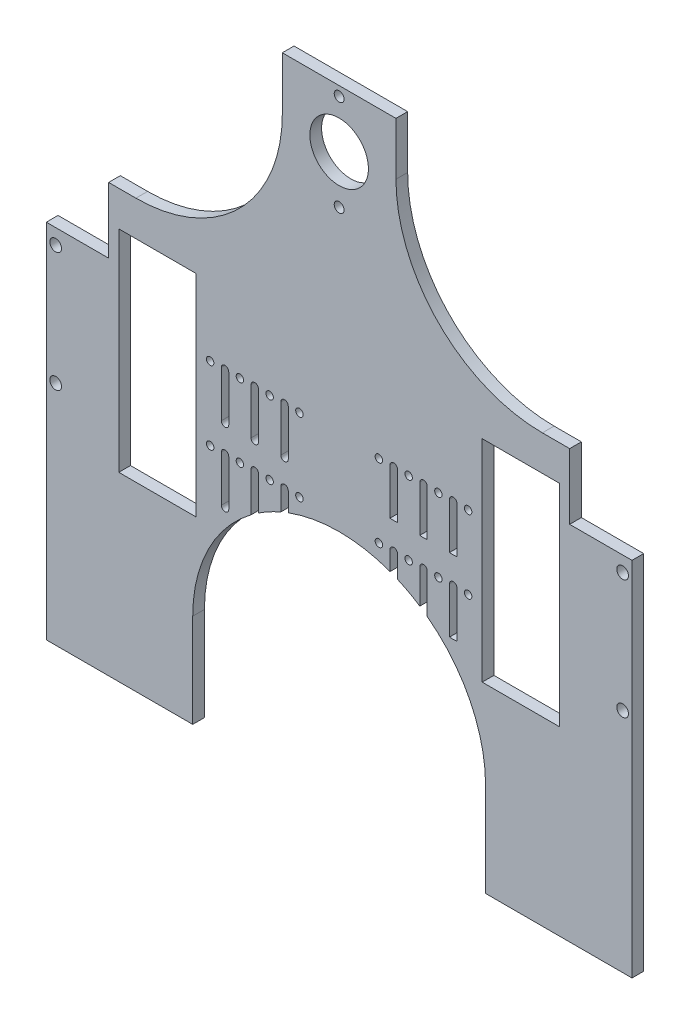
SolidWorks part; units mm, degrees
ref_plane "Front Plane" through (0, 0, 0) normal (0, 0, 1) x (1, 0, 0)
ref_plane "Top Plane" through (0, 0, 0) normal (0, 1, 0) x (1, 0, 0)
ref_plane "Right Plane" through (0, 0, 0) normal (1, 0, 0) x (0, 0, -1)
sketch "Sketch1" plane through (0, 0, 0) normal (0, 0, 1) x (1, 0, 0)
  line L0 (125, 0) -> (125, -350.4) construction
  line L1 (0, 0) -> (250, 0)
  line L2 (0, 0) -> (0, -350.4)
  line L3 (0, -350.4) -> (250, -350.4)
  line L4 (250, 0) -> (250, -350.4)
  line L9 (186.06, -100) -> (219.06, -100)
  line L10 (186.06, -100) -> (186.06, -190)
  line L11 (186.06, -190) -> (219.06, -190)
  line L12 (219.06, -100) -> (219.06, -190)
  line L13 (180.06, -145) -> (228.95, -145) construction
  line L14 (141.96, -129.375) -> (148.31, -129.375) construction
  line L21 (180.06, -145) -> (219.06, -145) construction
  line L25 (141.96, -160.625) -> (148.31, -160.625) construction
  line L32 (148.31, -129.375) -> (148.31, -134.375) construction
  line L33 (146.7225, -129.375) -> (146.7225, -149.0546)
  line L34 (149.8975, -129.375) -> (149.8975, -149.0546)
  line L35 (161.01, -129.375) -> (161.01, -134.375) construction
  line L36 (159.42, -129.375) -> (159.42, -149.0546)
  line L37 (162.6, -129.375) -> (162.6, -149.0546)
  line L38 (173.71, -129.375) -> (173.71, -134.375) construction
  line L39 (172.12, -129.375) -> (172.12, -149.0546)
  line L40 (175.3, -129.375) -> (175.3, -149.0546)
  line L41 (148.31, -129.375) -> (154.66, -129.375) construction
  line L42 (154.66, -129.375) -> (161.01, -129.375) construction
  line L43 (161.01, -129.375) -> (167.36, -129.375) construction
  line L44 (167.36, -129.375) -> (173.71, -129.375) construction
  line L45 (173.71, -129.375) -> (180.06, -129.375) construction
  line L48 (228.95, -145) -> (148.31, -145) construction
  line L52 (205.06, -100) -> (205.06, -190) construction
  line L53 (195.06, -100) -> (215.06, -100) construction
  line L54 (195.06, -100) -> (195.06, -190) construction
  line L55 (195.06, -190) -> (215.06, -190) construction
  line L56 (215.06, -100) -> (215.06, -190) construction
  line L62 (148.31, -160.625) -> (148.31, -165.625) construction
  line L65 (146.7225, -160.625) -> (146.7225, -180.3046)
  line L68 (149.8975, -160.625) -> (149.8975, -180.3046)
  line L71 (161.01, -160.625) -> (161.01, -165.625) construction
  line L78 (159.42, -160.625) -> (159.42, -180.3046)
  line L79 (162.6, -160.625) -> (162.6, -180.3046)
  line L80 (173.71, -160.625) -> (173.71, -165.625) construction
  line L83 (172.12, -160.625) -> (172.12, -180.3046)
  line L87 (148.31, -145) -> (101.69, -145) construction
  line L90 (180.06, -129.375) -> (180.06, -160.625) construction
  line L93 (148.31, -129.375) -> (148.31, -145) construction
  line L102 (246, -119.5) -> (246, -170.5) construction
  line L103 (219.06, -145) -> (246, -145) construction
  line L105 (175.3, -160.625) -> (175.3, -180.3046)
  line L106 (148.31, -160.625) -> (154.66, -160.625) construction
  line L107 (154.66, -160.625) -> (161.01, -160.625) construction
  line L108 (161.01, -160.625) -> (167.36, -160.625) construction
  line L109 (167.36, -160.625) -> (173.71, -160.625) construction
  line L110 (173.71, -160.625) -> (180.06, -160.625) construction
  line L111 (101.69, -129.375) -> (101.69, -149.0546) construction
  line L112 (103.2775, -129.375) -> (103.2775, -149.0546)
  line L113 (100.1025, -129.375) -> (100.1025, -149.0546)
  line L114 (88.99, -129.375) -> (88.99, -149.0546) construction
  line L115 (90.58, -129.375) -> (90.58, -149.0546)
  line L116 (87.4, -129.375) -> (87.4, -149.0546)
  line L117 (76.29, -129.375) -> (76.29, -149.0546) construction
  line L118 (77.88, -129.375) -> (77.88, -149.0546)
  line L119 (74.7, -129.375) -> (74.7, -149.0546)
  line L120 (101.69, -160.625) -> (101.69, -180.3046) construction
  line L121 (103.2775, -160.625) -> (103.2775, -180.3046)
  line L122 (100.1025, -160.625) -> (100.1025, -180.3046)
  line L123 (88.99, -160.625) -> (88.99, -180.3046) construction
  line L124 (90.58, -160.625) -> (90.58, -180.3046)
  line L125 (87.4, -160.625) -> (87.4, -180.3046)
  line L126 (76.29, -160.625) -> (76.29, -180.3046) construction
  line L127 (77.88, -160.625) -> (77.88, -180.3046)
  line L128 (74.7, -160.625) -> (74.7, -180.3046)
  line L129 (76.29, -160.625) -> (69.94, -160.625) construction
  line L130 (82.64, -160.625) -> (76.29, -160.625) construction
  line L131 (88.99, -160.625) -> (82.64, -160.625) construction
  line L132 (95.34, -160.625) -> (88.99, -160.625) construction
  line L133 (101.69, -160.625) -> (95.34, -160.625) construction
  line L134 (30.94, -145) -> (4, -145) construction
  line L135 (4, -119.5) -> (4, -170.5) construction
  line L136 (101.69, -129.375) -> (101.69, -145) construction
  line L137 (69.94, -129.375) -> (69.94, -160.625) construction
  line L139 (34.94, -100) -> (34.94, -190) construction
  line L140 (54.94, -190) -> (34.94, -190) construction
  line L141 (54.94, -100) -> (54.94, -190) construction
  line L142 (54.94, -100) -> (34.94, -100) construction
  line L143 (44.94, -100) -> (44.94, -190) construction
  line L144 (21.05, -145) -> (101.69, -145) construction
  line L145 (76.29, -129.375) -> (69.94, -129.375) construction
  line L146 (82.64, -129.375) -> (76.29, -129.375) construction
  line L147 (88.99, -129.375) -> (82.64, -129.375) construction
  line L148 (95.34, -129.375) -> (88.99, -129.375) construction
  line L149 (101.69, -129.375) -> (95.34, -129.375) construction
  line L150 (108.04, -160.625) -> (101.69, -160.625) construction
  line L151 (69.94, -145) -> (30.94, -145) construction
  line L152 (108.04, -129.375) -> (101.69, -129.375) construction
  line L153 (69.94, -145) -> (21.05, -145) construction
  line L154 (30.94, -100) -> (30.94, -190)
  line L155 (63.94, -190) -> (30.94, -190)
  line L156 (63.94, -100) -> (63.94, -190)
  line L157 (63.94, -100) -> (30.94, -100)
  arc A6 (175.3, -129.375) -> (172.12, -129.375) centre (173.71, -129.375) cw construction
  arc A7 (172.12, -129.375) -> (175.3, -129.375) centre (173.71, -129.375) cw
  arc A10 (159.42, -129.375) -> (162.6, -129.375) centre (161.01, -129.375) cw
  arc A11 (162.6, -129.375) -> (159.42, -129.375) centre (161.01, -129.375) cw construction
  arc A14 (146.7225, -129.375) -> (149.8975, -129.375) centre (148.31, -129.375) cw
  arc A15 (149.8975, -129.375) -> (146.7225, -129.375) centre (148.31, -129.375) cw construction
  arc A39 (149.8975, -149.0546) -> (146.7225, -149.0546) centre (148.31, -134.375) cw
  circle A40 centre (125, -45) radius 2.1
  arc A41 (162.6, -149.0546) -> (159.42, -149.0546) centre (161.01, -134.375) cw
  circle A42 centre (125, -4) radius 2.1
  arc A43 (175.3, -149.0546) -> (172.12, -149.0546) centre (173.71, -134.375) cw
  circle A84 centre (246, -119.5) radius 2.5
  circle A85 centre (246, -170.5) radius 2.5
  circle A179 centre (180.06, -129.375) radius 1.59
  arc A182 (175.3, -160.625) -> (172.12, -160.625) centre (173.71, -160.625) cw construction
  arc A183 (172.12, -160.625) -> (175.3, -160.625) centre (173.71, -160.625) cw
  arc A184 (159.42, -160.625) -> (162.6, -160.625) centre (161.01, -160.625) cw
  arc A185 (162.6, -160.625) -> (159.42, -160.625) centre (161.01, -160.625) cw construction
  arc A188 (146.7225, -160.625) -> (149.8975, -160.625) centre (148.31, -160.625) cw
  arc A189 (149.8975, -160.625) -> (146.7225, -160.625) centre (148.31, -160.625) cw construction
  arc A193 (149.8975, -180.3046) -> (146.7225, -180.3046) centre (148.31, -165.625) cw
  arc A195 (162.6, -180.3046) -> (159.42, -180.3046) centre (161.01, -165.625) cw
  arc A197 (175.3, -180.3046) -> (172.12, -180.3046) centre (173.71, -165.625) cw
  circle A198 centre (180.06, -160.625) radius 1.59
  circle A199 centre (125, -24.5) radius 12.5
  circle A200 centre (141.96, -129.375) radius 1.59
  circle A201 centre (154.66, -129.375) radius 1.59
  circle A202 centre (167.36, -129.375) radius 1.59
  circle A203 centre (141.96, -160.625) radius 1.59
  circle A204 centre (154.66, -160.625) radius 1.59
  circle A205 centre (167.36, -160.625) radius 1.59
  arc A206 (103.2775, -129.375) -> (100.1025, -129.375) centre (101.69, -129.375) ccw
  arc A207 (100.1025, -149.0546) -> (103.2775, -149.0546) centre (101.69, -149.0546) ccw
  arc A208 (90.58, -129.375) -> (87.4, -129.375) centre (88.99, -129.375) ccw
  arc A209 (87.4, -149.0546) -> (90.58, -149.0546) centre (88.99, -149.0546) ccw
  arc A210 (77.88, -129.375) -> (74.7, -129.375) centre (76.29, -129.375) ccw
  arc A211 (74.7, -149.0546) -> (77.88, -149.0546) centre (76.29, -149.0546) ccw
  arc A212 (103.2775, -160.625) -> (100.1025, -160.625) centre (101.69, -160.625) ccw
  arc A213 (100.1025, -180.3046) -> (103.2775, -180.3046) centre (101.69, -180.3046) ccw
  arc A214 (90.58, -160.625) -> (87.4, -160.625) centre (88.99, -160.625) ccw
  arc A215 (87.4, -180.3046) -> (90.58, -180.3046) centre (88.99, -180.3046) ccw
  arc A216 (77.88, -160.625) -> (74.7, -160.625) centre (76.29, -160.625) ccw
  arc A217 (74.7, -180.3046) -> (77.88, -180.3046) centre (76.29, -180.3046) ccw
  arc A218 (100.1025, -160.625) -> (103.2775, -160.625) centre (101.69, -160.625) ccw construction
  arc A219 (87.4, -160.625) -> (90.58, -160.625) centre (88.99, -160.625) ccw construction
  arc A220 (74.7, -160.625) -> (77.88, -160.625) centre (76.29, -160.625) ccw construction
  arc A221 (100.1025, -129.375) -> (103.2775, -129.375) centre (101.69, -129.375) ccw construction
  arc A222 (87.4, -129.375) -> (90.58, -129.375) centre (88.99, -129.375) ccw construction
  arc A223 (74.7, -129.375) -> (77.88, -129.375) centre (76.29, -129.375) ccw construction
  circle A224 centre (82.64, -160.625) radius 1.59
  circle A225 centre (95.34, -160.625) radius 1.59
  circle A226 centre (108.04, -160.625) radius 1.59
  circle A227 centre (82.64, -129.375) radius 1.59
  circle A228 centre (95.34, -129.375) radius 1.59
  circle A229 centre (108.04, -129.375) radius 1.59
  circle A230 centre (69.94, -160.625) radius 1.59
  circle A234 centre (69.94, -129.375) radius 1.59
  circle A236 centre (4, -170.5) radius 2.5
  circle A237 centre (4, -119.5) radius 2.5
  point P64 (148.31, -145)
  point P65 (101.69, -139.2148)
  point P69 (228.95, -145)
  point P71 (221, -87.34)
  point P76 (233.7, -87.34)
  point P78 (221, -54.5)
  point P82 (233.7, -54.5)
  point P86 (246.4, -54.5)
  point P93 (180.06, -145)
  point P97 (246.4, -87.34)
  point P104 (88.99, -139.2148)
  point P111 (76.29, -139.2148)
  point P119 (101.69, -170.4648)
  point P126 (88.99, -170.4648)
  point P133 (76.29, -170.4648)
  point P155 (125, -76.5574)
  point P166 (125, -145)
  point P183 (125, -76.5574)
  point P199 (69.94, -145)
  point P200 (21.05, -145)
  point P201 (101.69, -145)
  dimension "D5" = 20
  dimension "D10" = 5
  dimension "D12" = 3.18
  dimension "D15" = 5
  dimension "D16" = 5
  dimension "D19" = 3.18
  dimension "D20" = 1.5875
  dimension "D21" = 3.18
  dimension "D22" = 1.59
  dimension "D23" = 3.18
  dimension "D24" = 1.59
  dimension "D25" = 3.18
  dimension "D33" = 3.18
  dimension "D34" = 5
  dimension "D32" = 1.5875
  dimension "D36" = 1.59
  dimension "D37" = 3.18
  dimension "D39" = 1.59
  dimension "D47" = 3.18
  dimension "D49" = 25
  dimension "D53" = 4.2
  dimension "D54" = 4.2
  dimension "D1" = 250
  dimension "D2" = 350.4
  dimension "D3" = 4
  dimension "D4" = 90
  dimension "D6" = 90
  dimension "D7" = 9
  dimension "D8" = 6
  dimension "D9" = 5
  dimension "D11" = 6.35
  dimension "D13" = 6.35
  dimension "D14" = 90.06
  dimension "D17" = 25.5
  dimension "D18" = 4
  dimension "D26" = 5
  dimension "D27" = 6.35
  dimension "D28" = 6.35
  dimension "D29" = 6.35
  dimension "D30" = 6.35
  dimension "D31" = 6.35
  dimension "D38" = 100
  dimension "D40" = 5
  dimension "D41" = 6.35
  dimension "D42" = 6.35
  dimension "D43" = 6.35
  dimension "D44" = 6.35
  dimension "D45" = 6.35
  dimension "D46" = 5
  dimension "D48" = 31.25
  dimension "D52" = 20.5
  dimension "D55" = 4
  dimension "D56" = 20.5
extrude "Boss-Extrude1" add sketch "Sketch1" along normal blind 5
sketch "Sketch12" plane through (0, -350.4, 0) normal (0, -1, 0) x (1, 0, 0)
  line L0 (0, 0) -> (250, 0)
  line L1 (0, 0) -> (0, 5)
  line L2 (250, 0) -> (250, 5)
  line L3 (0, 5) -> (250, 5)
  line L5 (0, 5) -> (250, 5) construction
extrude "Cut-Extrude2" cut sketch "Sketch12" against normal blind 83
sketch "Sketch14" plane through (0, 0, 5) normal (0, 0, 1) x (1, 0, 0)
  line L0 (-135.3499, -267.4) -> (537.3728, -267.4) construction
  line L1 (250, -267.4) -> (0, -267.4) construction
sketch "Sketch11" plane through (0, 0, 5) normal (0, 0, 1) x (1, 0, 0)
  line L1 (0, 0) -> (0, -267.4) construction
  line L2 (250, -267.4) -> (250, 0) construction
  line L3 (0, -95) -> (250, -95) construction
  line L6 (-135.3499, -267.4) -> (537.3728, -267.4) construction
  line L8 (250, 0) -> (0, 0) construction
  line L9 (190, 0) -> (190, -350.4) construction
  line L10 (245, 0) -> (245, -350.4) construction
  line L11 (185, 0) -> (185, -350.4) construction
  line L19 (0, -100) -> (250, -100) construction
  line L20 (234.9216, -93.9797) -> (234.9216, -98.9797) construction
  line L22 (125, 0) -> (125, -350.4) construction
  line L23 (63.94, -100) -> (30.94, -100) construction
  line L27 (162.6, -149.0546) -> (162.6, -129.375) construction
  line L30 (74.7, -129.375) -> (74.7, -149.0546) construction
  line L31 (5, -350.4) -> (5, 0) construction
  line L33 (65, -350.4) -> (65, 0) construction
  line L34 (-280.106, -400.8809) -> (540.7046, 73.0144) construction
  line L35 (60, 0) -> (60, -350.4) construction
  line L36 (-311.7759, -280.6014) -> (435.1808, 150.6543) construction
  line L37 (382.7004, -177.2121) -> (-155.9503, 133.778) construction
  line L38 (371.0091, -309.0262) -> (-242.9221, 45.4271) construction
  line L39 (15.0784, -93.9797) -> (15.0784, -98.9797) construction
  line L40 (15.0784, -93.9797) -> (106.287, -15.999) construction
  line L41 (122.3685, -34.8084) -> (83.2439, 10.953) construction
  line L42 (234.9216, -93.9797) -> (143.713, -15.999) construction
  line L43 (127.6315, -34.8084) -> (166.7561, 10.953) construction
  line L44 (0, -164.9) -> (250, -164.9) construction
  line L45 (0, 0) -> (0, -267.4) construction
  line L46 (250, -267.4) -> (250, 0) construction
  circle A11 centre (125, -227.4) radius 60 construction
  circle A12 centre (125, -227.4) radius 62.5 construction
  circle A13 centre (209.62, -146.5661) radius 24.62 construction
  circle A14 centre (82.69, -73.2831) radius 60 construction
  circle A15 centre (125, 0) radius 24.62 construction
  circle A17 centre (40.38, -146.5661) radius 24.62 construction
  circle A18 centre (167.31, -73.2831) radius 60 construction
  circle A19 centre (209.62, -267.4) radius 24.62 construction
  circle A20 centre (40.38, -267.4) radius 24.62 construction
  dimension "D4" = 5
  dimension "D5" = 125
  dimension "D3" = 120
  dimension "D9" = 5
  dimension "D10" = 120
  dimension "D11" = 5
  dimension "D12" = 5
  dimension "D13" = 49.24
  dimension "D14" = 5
  dimension "D16" = 49.24
  dimension "D8" = 49.24
  dimension "D15" = 120
  dimension "D6" = 120
  dimension "D2" = 49.24
  dimension "D7" = 5
  dimension "D17" = 40
sketch "Sketch13" plane through (0, 0, 5) normal (0, 0, 1) x (1, 0, 0)
  line L0 (26.6043, -85) -> (211.7496, -85) construction
  line L1 (38.2504, -85) -> (26.6043, -85)
  line L5 (250, 0) -> (250, -113)
  line L6 (0, -100) -> (36, -100) construction
  line L7 (63.94, -100) -> (30.94, -100) construction
  line L8 (0, 0) -> (0, -267.4) construction
  line L9 (-135.3499, -267.4) -> (537.3728, -267.4) construction
  line L10 (250, -267.4) -> (250, 0) construction
  line L12 (62.5, -227.4) -> (62.5, -350.4)
  line L14 (62.5, -350.4) -> (187.5, -350.4)
  line L15 (187.5, -227.4) -> (187.5, -350.4)
  line L16 (250, 0) -> (153.4401, 0)
  line L17 (60, 0) -> (60, -350.4) construction
  line L20 (96.5599, 0) -> (0, 0)
  line L21 (250, 0) -> (0, 0) construction
  line L31 (223.3957, -85) -> (223.3957, -113)
  line L32 (250, -113) -> (223.3957, -113)
  line L33 (211.7496, -85) -> (223.3957, -85)
  line L35 (125, 0) -> (125, -350.4) construction
  line L36 (0, -113) -> (26.6043, -113)
  line L37 (26.6043, -85) -> (26.6043, -113)
  line L38 (0, 0) -> (0, -113)
  arc A0 (38.2504, -85) -> (96.5599, 0) centre (38.2504, -22.5) ccw
  arc A1 (153.4401, 0) -> (211.7496, -85) centre (211.7496, -22.5) ccw
  circle A2 centre (38.2504, -22.5) radius 65 construction
  arc A3 (250, -75.0539) -> (223.3957, -86.4482) centre (211.7496, -22.5) ccw construction
  circle A4 centre (125, 0) radius 24.62 construction
  arc A5 (187.5, -227.4) -> (62.5, -227.4) centre (125, -227.4) ccw
  circle A6 centre (125, -227.4) radius 62.5 construction
  dimension "D2" = 130
  dimension "D3" = 62.5
  dimension "D4" = 130
  dimension "D5" = 62.5
  dimension "D1" = 15
  dimension "D6" = 154.4
  dimension "D8" = 26.6043
extrude "Cut-Extrude3" cut sketch "Sketch13" against normal through all
sketch "Sketch15" plane through (0, 0, 5) normal (0, 0, 1) x (1, 0, 0)
  line L0 (149.2496, 13.1038) -> (149.2496, -22.5) construction
  line L1 (100.7504, 16.9922) -> (100.7504, -22.5) construction
  line L2 (153.4401, 0) -> (96.5599, 0) construction
  line L3 (100.7504, -22.5) -> (100.7504, 0)
  line L4 (100.7504, -22.5) -> (80.4559, -22.5)
  line L5 (100.7504, 0) -> (80.4559, 0)
  line L6 (80.4559, -22.5) -> (80.4559, 0)
  line L7 (149.2496, -22.5) -> (149.2496, 0)
  line L8 (149.2496, -22.5) -> (165.496, -22.5)
  line L9 (149.2496, 0) -> (165.496, 0)
  line L10 (165.496, -22.5) -> (165.496, 0)
  arc A0 (38.2504, -85) -> (96.5599, 0) centre (38.2504, -22.5) ccw construction
  arc A1 (153.4401, 0) -> (211.7496, -85) centre (211.7496, -22.5) ccw construction
extrude "Cut-Extrude4" cut sketch "Sketch15" against normal blind 10
